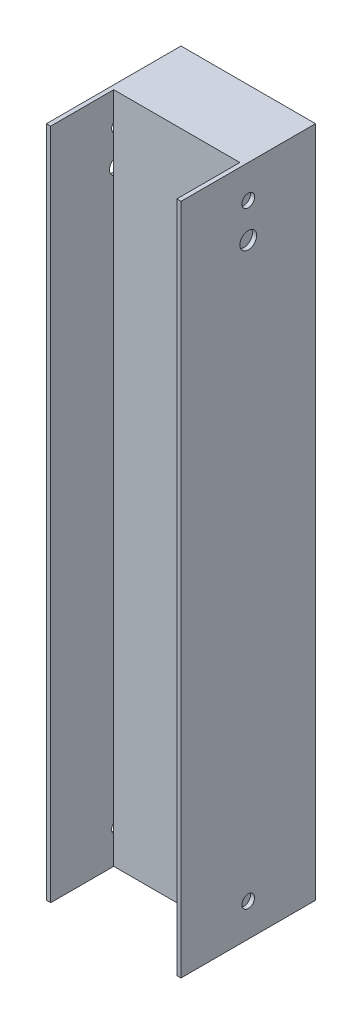
SolidWorks part; units mm, degrees
material "6061 Alloy"
ref_plane "Front Plane" through (0, 0, 0) normal (0, 0, 1) x (1, 0, 0)
ref_plane "Top Plane" through (0, 0, 0) normal (0, 1, 0) x (1, 0, 0)
ref_plane "Right Plane" through (0, 0, 0) normal (1, 0, 0) x (0, 0, -1)
sketch "Sketch1" plane through (0, 0, 0) normal (0, 1, 0) x (1, 0, 0)
  line L1 (-23.8125, 23.8125) -> (23.8125, 23.8125)
  line L2 (-23.8125, 23.8125) -> (-23.8125, -23.8125)
  line L3 (-23.8125, -23.8125) -> (23.8125, -23.8125)
  line L4 (23.8125, 23.8125) -> (23.8125, -23.8125)
  line L5 (-25.4, 25.4) -> (25.4, 25.4)
  line L6 (-25.4, 25.4) -> (-25.4, -25.4)
  line L7 (-25.4, -25.4) -> (25.4, -25.4)
  line L8 (25.4, 25.4) -> (25.4, -25.4)
  point P2 (-25.4, 0)
  point P11 (-23.8125, 0)
  point P12 (0, 23.8125)
  point P13 (0, 25.4)
  dimension "D1" = 47.625
  dimension "1.95" = 47.625
  dimension "2.05" = 50.8
  dimension "D2" = 50.8
extrude "Boss-Extrude1" add sketch "Sketch1" along normal blind 254
ref_plane "Plane1" through (0, 152.4, 0) normal (0, 1, 0) x (1, 0, 0)
sketch "Sketch4" plane through (-23.8125, 0, 0) normal (1, 0, 0) x (0, 0, -1)
  line L0 (-25.4, 254) -> (25.4, 254) construction
  line L1 (25.4, 254) -> (25.4, 0) construction
  circle A0 centre (0, 241.5876) radius 2.4
  dimension "D1" = 4.8
  dimension "D2" = 12.4124
  dimension "D3" = 25.4
extrude "Cut-Extrude1" cut sketch "Sketch4" along normal through all both and the other way through all
sketch "Sketch5" plane through (0, 0, -25.4) normal (0, 0, -1) x (-1, 0, 0)
  line L0 (-25.4, 254) -> (25.4, 254) construction
  line L1 (25.4, 254) -> (25.4, 0) construction
  circle A0 centre (0, 241.5876) radius 2.4
  dimension "D1" = 4.8
  dimension "D2" = 12.4124
  dimension "D3" = 25.4
extrude "Cut-Extrude2" cut sketch "Sketch5" against normal through all
sketch "Sketch6" plane through (25.4, 0, 0) normal (1, 0, 0) x (0, 0, -1)
  line L0 (-25.4, 0) -> (25.4, 0) construction
  line L1 (25.4, 254) -> (25.4, 0) construction
  circle A0 centre (0, 12.4124) radius 2.4
  dimension "D1" = 12.4124
  dimension "D2" = 4.8
  dimension "D3" = 25.4
extrude "Cut-Extrude3" cut sketch "Sketch6" against normal through all both and the other way through all
sketch "Sketch7" plane through (0, 0, -25.4) normal (0, 0, -1) x (-1, 0, 0)
  line L0 (-25.4, 0) -> (25.4, 0) construction
  circle A0 centre (0, 12.4124) radius 2.4
  dimension "D1" = 4.8
  dimension "D2" = 12.4124
  dimension "D3" = 25.4
extrude "Cut-Extrude4" cut sketch "Sketch7" against normal through all both
sketch "Sketch8" plane through (0, 0, -25.4) normal (0, 0, -1) x (-1, 0, 0)
  line L0 (-25.4, 254) -> (25.4, 254) construction
  line L1 (-25.4, 254) -> (-25.4, 0) construction
  circle A0 centre (0, 228.6) radius 3.175
  dimension "D1" = 6.35
  dimension "D2" = 25.4
  dimension "D3" = 25.4
extrude "Cut-Extrude5" cut sketch "Sketch8" against normal through all both and the other way through all
sketch "Sketch9" plane through (25.4, 0, 0) normal (1, 0, 0) x (0, 0, -1)
  line L0 (-25.4, 254) -> (25.4, 254) construction
  line L1 (-25.4, 254) -> (-25.4, 0) construction
  circle A0 centre (0, 228.6) radius 3.175
  dimension "D1" = 6.35
  dimension "D2" = 25.4
  dimension "D3" = 25.4
extrude "Cut-Extrude6" cut sketch "Sketch9" against normal through all both
sketch "Sketch10" plane through (0, 0, 0) normal (0, -1, 0) x (1, 0, 0)
  line L0 (-25.4, 25.4) -> (25.4, 25.4) construction
  line L1 (-23.8125, 23.8125) -> (23.8125, 23.8125)
  line L2 (-23.8125, 23.8125) -> (-23.8125, 25.4)
  line L3 (-23.8125, 25.4) -> (23.8125, 25.4)
  line L4 (23.8125, 23.8125) -> (23.8125, 25.4)
extrude "Cut-Extrude7" cut sketch "Sketch10" against normal up to next
sketch "Sketch11" plane through (0, 0, 0) normal (0, -1, 0) x (1, 0, 0)
  line L0 (23.8125, 25.4) -> (23.8125, -23.8125) construction
  line L1 (-23.8125, -23.8125) -> (23.8125, -23.8125)
  line L2 (-23.8125, -23.8125) -> (-23.8125, 1.5875)
  line L3 (-23.8125, 1.5875) -> (23.8125, 1.5875)
  line L4 (23.8125, -23.8125) -> (23.8125, 1.5875)
  dimension "D1" = 25.4
extrude "Boss-Extrude2" add sketch "Sketch11" against normal through all
equation "\"1.95@Sketch1\"=2-(1/8)"
equation "\"D1@Sketch1\"=\"1.95@Sketch1\""
